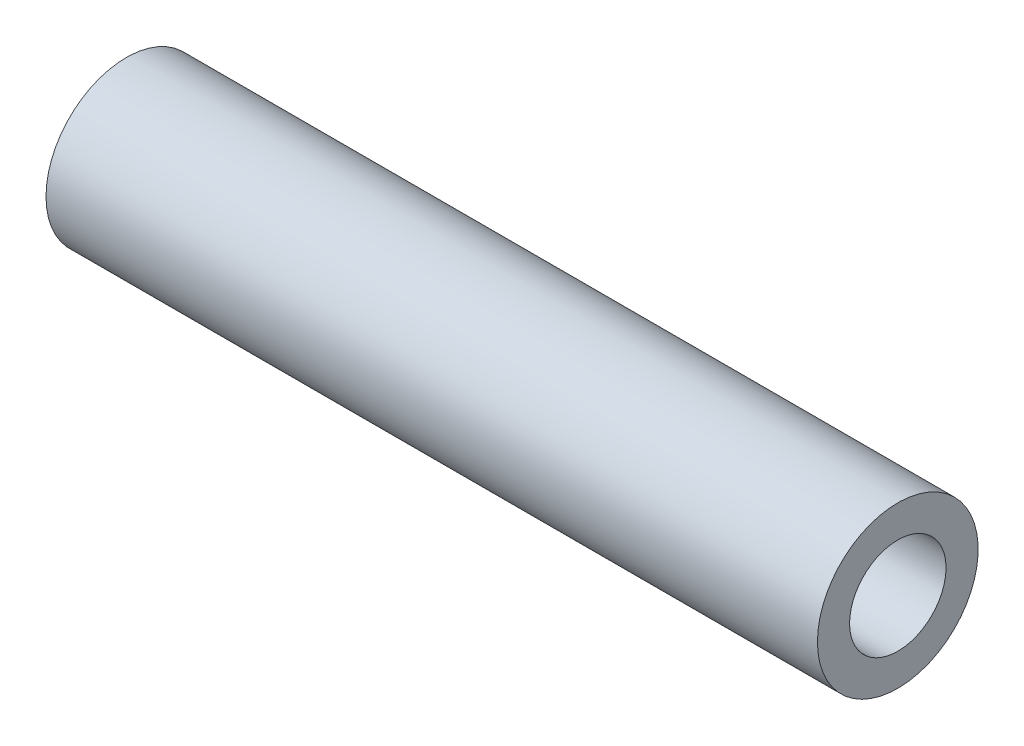
SolidWorks part; units mm, degrees
material "6061 Alloy"
ref_plane "Front Plane" through (0, 0, 0) normal (0, 0, 1) x (1, 0, 0)
ref_plane "Top Plane" through (0, 0, 0) normal (0, 1, 0) x (1, 0, 0)
ref_plane "Right Plane" through (0, 0, 0) normal (1, 0, 0) x (0, 0, -1)
sketch "Sketch1" plane through (0, 0, 0) normal (0, 0, 1) x (1, 0, 0)
  line L0 (0, 0) -> (75.7031, 0) construction
  line L1 (0, 12.7) -> (203.2, 12.7)
  line L2 (0, 12.7) -> (0, 21.1667)
  line L3 (0, 21.1667) -> (203.2, 21.1667)
  line L4 (203.2, 12.7) -> (203.2, 21.1667)
  dimension "D1" = 12.7
  dimension "D2" = 8.4667
  dimension "D3" = 203.2
revolve "Revolve1" add sketch "Sketch1" angle 360 about L0
